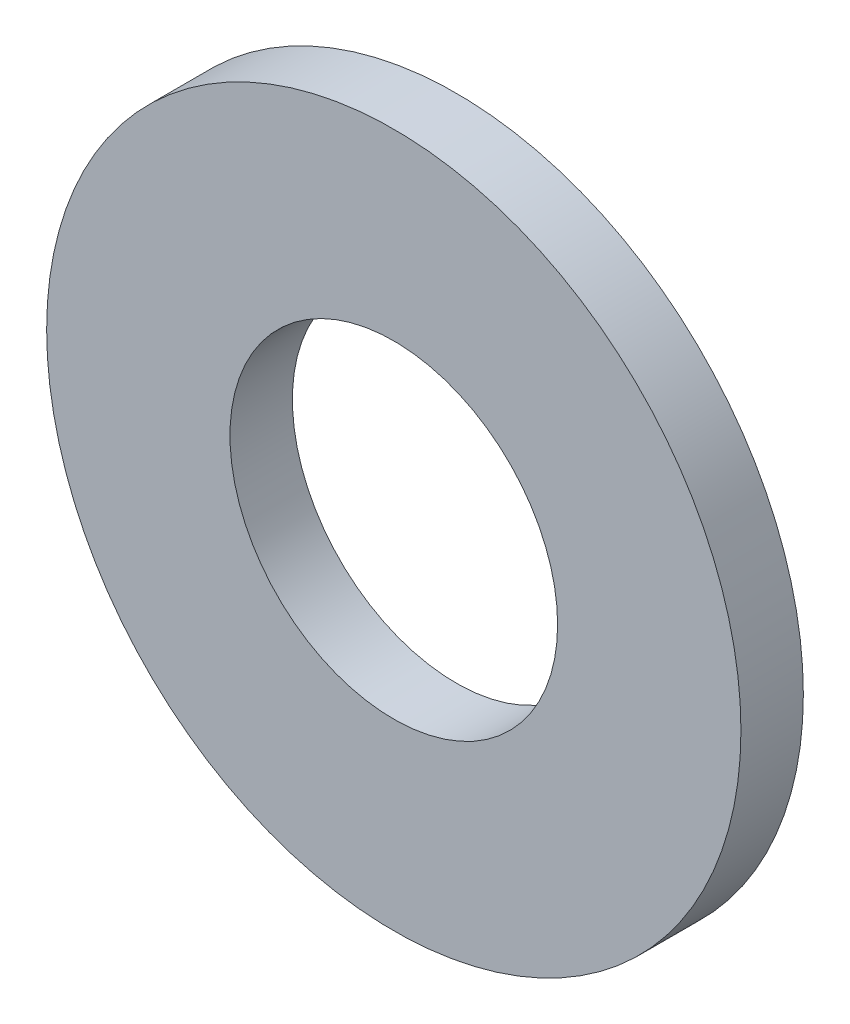
SolidWorks part; units mm, degrees
ref_plane "Front Plane" through (0, 0, 0) normal (0, 0, 1) x (1, 0, 0)
ref_plane "Top Plane" through (0, 0, 0) normal (0, 1, 0) x (1, 0, 0)
ref_plane "Right Plane" through (0, 0, 0) normal (1, 0, 0) x (0, 0, -1)
sketch "Sketch1" plane through (0, 0, 0) normal (0, 0, 1) x (1, 0, 0)
  circle A0 centre (0, 0) radius 4.45
  circle A1 centre (0, 0) radius 2.1
extrude "Extrude1" add sketch "Sketch1" against normal blind 0.8
